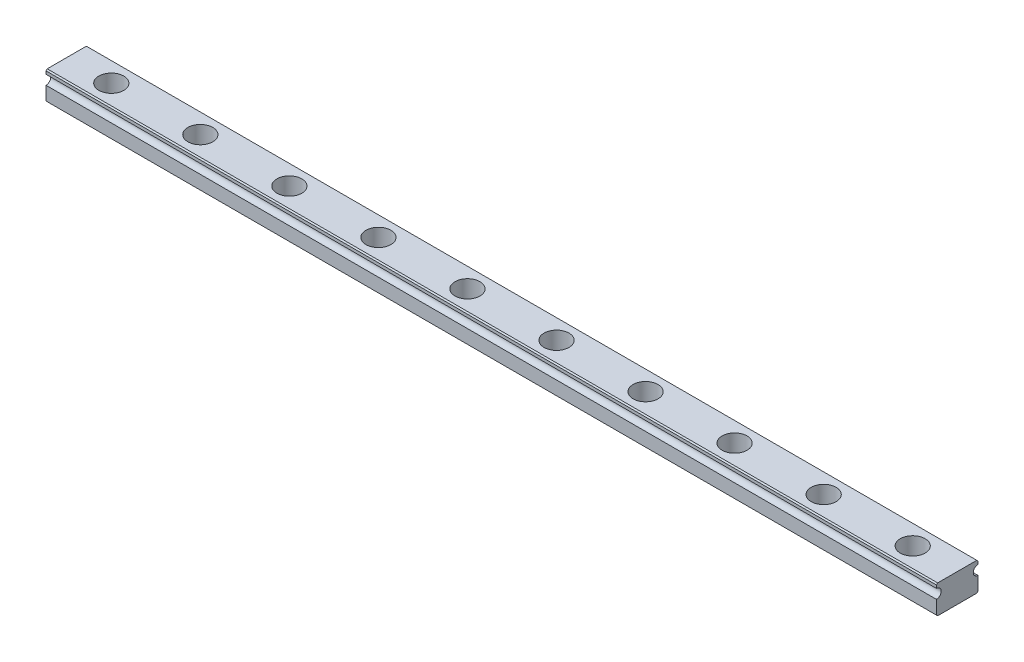
SolidWorks part; units mm, degrees
ref_plane "Plano frontal" through (0, 0, 0) normal (0, 0, 1) x (1, 0, 0)
ref_plane "Plano superior" through (0, 0, 0) normal (0, 1, 0) x (1, 0, 0)
ref_plane "Plano direito" through (0, 0, 0) normal (1, 0, 0) x (0, 0, -1)
sketch "Esboço1" plane through (0, 0, 0) normal (1, 0, 0) x (0, 0, -1)
  line L0 (-3.5, 0) -> (3.5, 0)
  line L1 (3.5, 0) -> (3.5, 2.5)
  line L2 (3.5, 4.1) -> (3.5, 4.8)
  line L3 (3.5, 4.8) -> (-3.5, 4.8)
  line L4 (0, 4.8) -> (0, 0) construction
  line L5 (-3.5, 4.1) -> (-3.5, 4.8)
  line L6 (-3.5, 0) -> (-3.5, 2.5)
  arc A0 (3.5, 2.5) -> (3.5, 4.1) centre (3.5, 3.3) cw
  arc A1 (-3.5, 2.5) -> (-3.5, 4.1) centre (-3.5, 3.3) ccw
  point P4 (0, 0)
  dimension "D4" = 0.8
  dimension "D1" = 3.3
  dimension "D2" = 1.5
  dimension "D3" = 7
extrude "Ressalto-extrusão1" add sketch "Esboço1" along normal mid plane 150
chamfer "Chanfro1" distance 0.2 angle 45 4 edges at (0, 4.8, -3.5) (0, 0, -3.5) (0, 0, 3.5) (0, 4.8, 3.5)
sketch "Esboço2" plane through (0, 4.8, 0) normal (0, 1, 0) x (1, 0, 0)
  line L0 (0, 0) -> (0, 28.412) construction
  circle A0 centre (-7.5, 0) radius 2.1
  circle A1 centre (-22.5, 0) radius 2.1
  circle A2 centre (-37.5, 0) radius 2.1
  circle A3 centre (-52.5, 0) radius 2.1
  circle A4 centre (-67.5, 0) radius 2.1
  circle A5 centre (67.5, 0) radius 2.1
  circle A6 centre (52.5, 0) radius 2.1
  circle A7 centre (37.5, 0) radius 2.1
  circle A8 centre (22.5, 0) radius 2.1
  circle A9 centre (7.5, 0) radius 2.1
  dimension "D2" = 4.2
  dimension "D1" = 15
  dimension "D3" = 5
extrude "Corte-extrusão1" cut sketch "Esboço2" against normal blind 150
